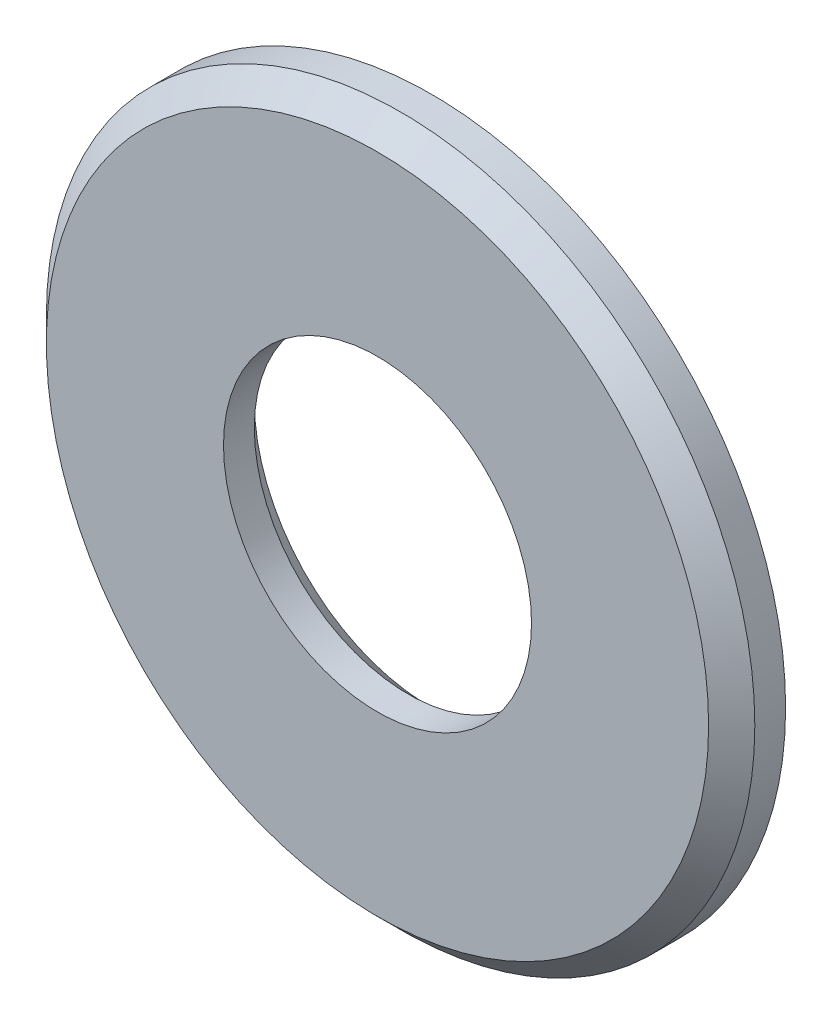
SolidWorks part; units mm, degrees
material "PA Type 6"
ref_plane "Plan de face" through (0, 0, 0) normal (0, 0, 1) x (1, 0, 0)
ref_plane "Plan de dessus" through (0, 0, 0) normal (0, 1, 0) x (1, 0, 0)
ref_plane "Plan de droite" through (0, 0, 0) normal (1, 0, 0) x (0, 0, -1)
sketch "Esquisse1" plane through (0, 0, 0) normal (0, 0, 1) x (1, 0, 0)
  circle A0 centre (0, 0) radius 23
  circle A1 centre (0, 0) radius 10
extrude "Boss.-Extru.1" add sketch "Esquisse1" along normal blind 3.5
chamfer "Chanfrein1" distance 1.5 angle 45 2 edges at (23, 0, 3.5) (10, 0, 0)
